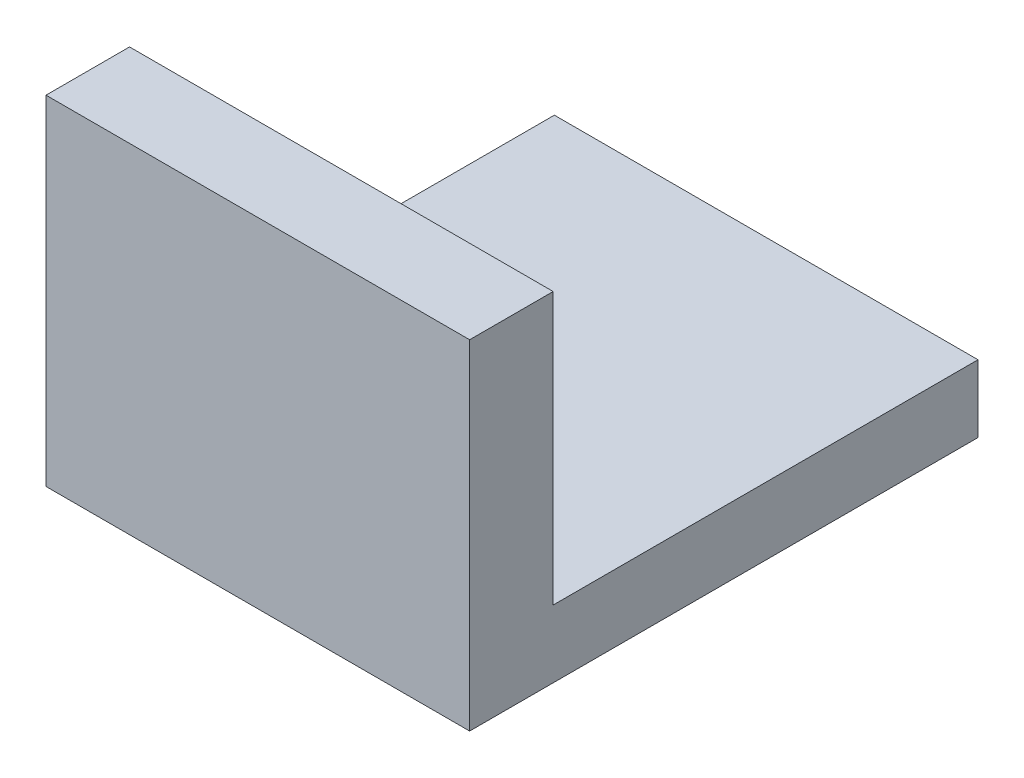
SolidWorks part; units mm, degrees
material "5052-H36"
ref_plane "Front Plane" through (0, 0, 0) normal (0, 0, 1) x (1, 0, 0)
ref_plane "Top Plane" through (0, 0, 0) normal (0, 1, 0) x (1, 0, 0)
ref_plane "Right Plane" through (0, 0, 0) normal (1, 0, 0) x (0, 0, -1)
sketch "Sketch2" plane through (0, 0, 0) normal (1, 0, 0) x (0, 0, -1)
  line L0 (0, 0) -> (0, 101.6)
  line L1 (0, 0) -> (152.4, 0)
  line L2 (152.4, 0) -> (152.4, 20.2064)
  line L3 (152.4, 20.2064) -> (25.0446, 20.2064)
  line L4 (25.0446, 20.2064) -> (25.0446, 101.6)
  line L5 (25.0446, 101.6) -> (0, 101.6)
  dimension "D1" = 101.6
  dimension "D2" = 152.4
extrude "Boss-Extrude1" add sketch "Sketch2" along normal blind 127
